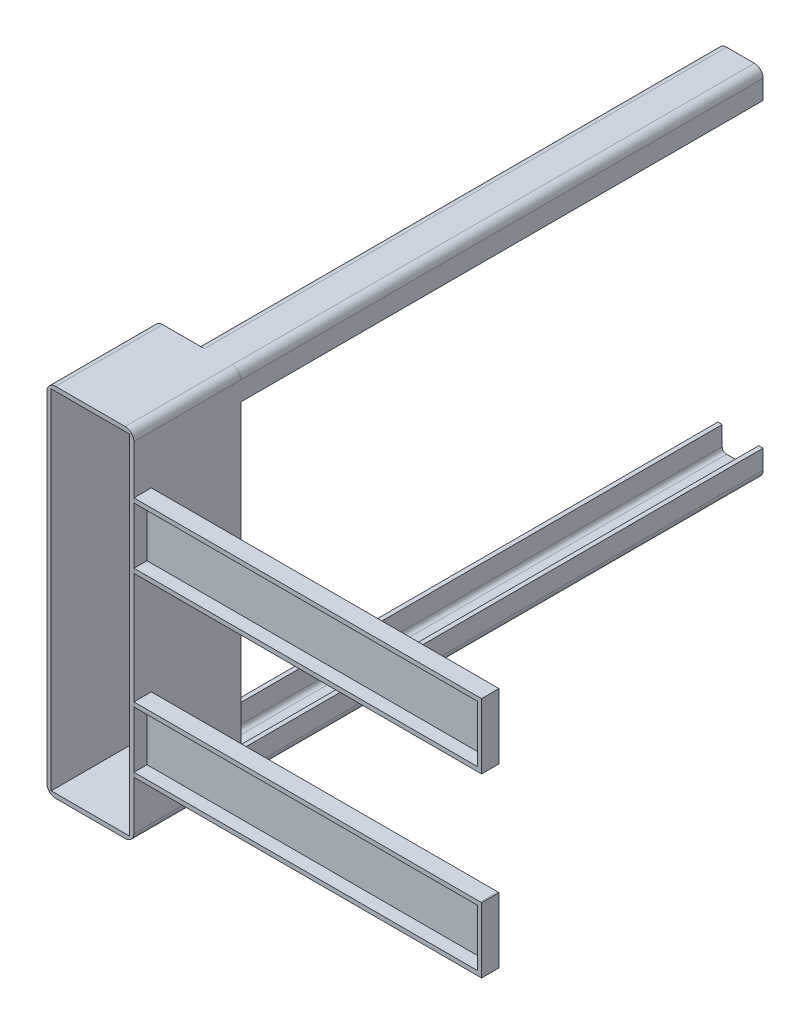
SolidWorks part; units mm, degrees
material "Alloy Steel"
ref_plane "Front Plane" through (0, 0, 0) normal (0, 0, 1) x (1, 0, 0)
ref_plane "Top Plane" through (0, 0, 0) normal (0, 1, 0) x (1, 0, 0)
ref_plane "Right Plane" through (0, 0, 0) normal (1, 0, 0) x (0, 0, -1)
sketch "Sketch1" plane through (0, 0, 0) normal (0, 0, 1) x (1, 0, 0)
  line L16 (-21, 173) -> (-26, 173)
  line L17 (16, 205) -> (-16, 205)
  line L18 (26, 195) -> (26, 173)
  line L19 (26, 173) -> (21, 173)
  line L20 (-26, 195) -> (-26, 173)
  line L21 (16, 200) -> (-16, 200)
  line L22 (21, 195) -> (21, 173)
  line L24 (-21, 195) -> (-21, 173)
  line L25 (0, 0) -> (0, 173) construction
  line L27 (-39.3633, 0) -> (62.171, 0) construction
  line L29 (-21, 173) -> (21, 173) construction
  line L30 (26, -195) -> (26, -173)
  line L31 (26, -173) -> (21, -173)
  line L32 (21, -195) -> (21, -173)
  line L33 (-21, -173) -> (-26, -173)
  line L34 (16, -205) -> (-16, -205)
  line L35 (16, -200) -> (-16, -200)
  line L36 (-26, -195) -> (-26, -173)
  line L37 (-21, -195) -> (-21, -173)
  arc A16 (26, 195) -> (16, 205) centre (16, 195) ccw
  arc A17 (-26, 195) -> (-16, 205) centre (-16, 195) cw
  arc A41 (16, 200) -> (21, 195) centre (16, 195) cw
  arc A42 (-16, 200) -> (-21, 195) centre (-16, 195) ccw
  arc A43 (16, -200) -> (21, -195) centre (16, -195) ccw
  arc A44 (26, -195) -> (16, -205) centre (16, -195) cw
  arc A45 (-26, -195) -> (-16, -205) centre (-16, -195) ccw
  arc A46 (-16, -200) -> (-21, -195) centre (-16, -195) cw
  point P34 (26, 205)
  point P39 (26, 173)
  point P44 (-21, 173)
  dimension "D5" = 10
  dimension "D8" = 32
  dimension "D3" = 5
  dimension "D6" = 52
  dimension "D11" = 205
extrude "Boss-Extrude1" add sketch "Sketch1" along normal blind 600
sketch "Sketch2" plane through (0, 0, 600) normal (0, 0, 1) x (1, 0, 0)
  line L27 (26, 205) -> (-74, 205)
  line L28 (26, 205) -> (26, -205)
  line L29 (26, -205) -> (-74, -205)
  line L30 (-74, 205) -> (-74, -205)
  line L31 (26, -195) -> (26, -173) construction
  line L32 (-16, -205) -> (16, -205) construction
  line L33 (16, 205) -> (-16, 205) construction
  dimension "D1" = 100
extrude "Boss-Extrude2" add sketch "Sketch2" along normal blind 123
sketch "Sketch37" plane through (0, 0, 600) normal (0, 0, -1) x (-1, 0, 0)
  line L0 (-26, -205) -> (-26, 173) construction
  line L1 (-26, 205) -> (74, 205) construction
  line L3 (-4, 54) -> (50, 54) construction
  line L4 (-4, 54) -> (-4, -142) construction
  line L5 (-4, -142) -> (50, -142) construction
  line L6 (50, 54) -> (50, -142) construction
  circle A0 centre (-4, -142) radius 10
  circle A1 centre (-4, 54) radius 10
  circle A2 centre (50, 54) radius 10
  circle A3 centre (50, -142) radius 10
  point P0 (-4, -142)
  dimension "D3" = 20
  dimension "D4" = 20
  dimension "D1" = 151
  dimension "D2" = 54
  dimension "D6" = 22
  dimension "D5" = 196
sketch "Sketch43" plane through (0, 0, 723) normal (0, 0, 1) x (1, 0, 0)
  line L1 (-69, 200) -> (21, 200)
  line L2 (-69, 200) -> (-69, -200)
  line L3 (-69, -200) -> (21, -200)
  line L4 (21, 200) -> (21, -200)
  line L8 (26, 205) -> (-74, 205) construction
  line L9 (26, -205) -> (26, 205) construction
  line L10 (-74, 205) -> (-74, -205) construction
  line L11 (-74, -205) -> (26, -205) construction
  dimension "D1" = 5
  dimension "D2" = 5
  dimension "D3" = 5
  dimension "D4" = 5
sketch "Sketch44" plane through (26, 0, 0) normal (1, 0, 0) x (0, 0, -1)
  line L1 (-723, 139) -> (-703, 139)
  line L2 (-723, 139) -> (-723, 64)
  line L3 (-723, 64) -> (-703, 64)
  line L4 (-703, 139) -> (-703, 64)
  line L5 (-723, 0) -> (-582.6794, 0)
  line L6 (-703, -139) -> (-703, -64)
  line L7 (-723, -64) -> (-703, -64)
  line L8 (-723, -139) -> (-723, -64)
  line L9 (-723, -139) -> (-703, -139)
  dimension "D1" = 75
  dimension "D2" = 20
  dimension "D3" = 64
extrude "Boss-Extrude16" add sketch "Sketch44" along normal blind 399.5
sketch "Sketch45" plane through (0, 139, 0) normal (0, 1, 0) x (1, 0, 0)
  line L2 (425.5, -703) -> (26, -703) construction
  line L3 (310.0576, -763.7413) -> (374.4424, -763.7413)
  line L5 (357.4487, -703) -> (327.0513, -703)
  arc A0 (327.0513, -703) -> (310.0576, -763.7413) centre (342.25, -740) ccw
  arc A1 (374.4424, -763.7413) -> (357.4487, -703) centre (342.25, -740) ccw
  point P1 (342.25, -740)
  dimension "D2" = 80
  dimension "D1" = 37
extrude "Boss-Extrude17" add sketch "Sketch45" against normal blind 278
sketch "Sketch47" plane through (0, 139, 0) normal (0, 1, 0) x (1, 0, 0)
  circle A0 centre (342.25, -740) radius 10
  dimension "D1" = 20
sketch "Sketch50" plane through (0, 0, 703) normal (0, 0, -1) x (-1, 0, 0)
  line L0 (-310.0576, 139) -> (-374.4424, 139) construction
  line L2 (-17.75, 0) -> (-475.9281, 0)
  line L3 (-383.75, 69) -> (-300.75, 69)
  line L4 (-383.75, 69) -> (-383.75, 134)
  line L5 (-383.75, 134) -> (-300.75, 134)
  line L6 (-300.75, 69) -> (-300.75, 134)
  line L7 (-383.75, 69) -> (-300.75, 134) construction
  line L8 (-383.75, 134) -> (-300.75, 69) construction
  line L10 (-383.75, -134) -> (-300.75, -69) construction
  line L11 (-383.75, -69) -> (-300.75, -134) construction
  line L12 (-300.75, -69) -> (-300.75, -134)
  line L13 (-383.75, -134) -> (-300.75, -134)
  line L14 (-383.75, -69) -> (-383.75, -134)
  line L15 (-383.75, -69) -> (-300.75, -69)
  point P0 (-342.25, 101.5)
  point P4 (-342.25, 101.5)
  point P18 (-342.25, -101.5)
  dimension "D1" = 5
  dimension "D2" = 65
  dimension "D3" = 83
extrude "Cut-Extrude19" cut sketch "Sketch37" against normal up to next (123 mm away) contours L5 A3 L6 | L6 A3 L5 | L4 A0 L5 | L5 A0 L4 | L6 A2 L3 | L3 A2 L6 | L4 A1 L3 | L3 A1 L4
extrude "Cut-Extrude20" cut sketch "Sketch43" against normal blind 118
extrude "Cut-Extrude21" cut sketch "Sketch47" against normal blind 278
sketch "Sketch54" plane through (26, 0, 0) normal (1, 0, 0) x (0, 0, -1)
  line L0 (-763.7413, -139) -> (-763.7413, 139) construction
  line L1 (-763.7413, 134) -> (-708, 134)
  line L2 (-763.7413, 134) -> (-763.7413, 69)
  line L3 (-763.7413, 69) -> (-708, 69)
  line L4 (-708, 134) -> (-708, 69)
  line L5 (-723, -64) -> (-703, -64) construction
  line L6 (-703, 139) -> (-703, 64) construction
  line L7 (-723, 64) -> (-703, 64) construction
  line L8 (-723, 139) -> (-763.7413, 139) construction
  line L9 (-708, -134) -> (-708, -69)
  line L10 (-767.5036, -69) -> (-708, -69)
  line L11 (-767.5036, -134) -> (-767.5036, -69)
  line L12 (-767.5036, -134) -> (-708, -134)
  line L13 (-703, -139) -> (-703, -64) construction
  line L14 (-723, -139) -> (-703, -139) construction
  dimension "D1" = 5
  dimension "D2" = 5
  dimension "D3" = 5
  dimension "D4" = 5
  dimension "D5" = 5
  dimension "D6" = 5
extrude "Cut-Extrude22" cut sketch "Sketch54" along normal blind 395
extrude "Cut-Extrude25" cut sketch "Sketch50" against normal blind 72 contours L3 L6 L5 L4 | L15 L14 L13 L12
sketch "Sketch55" plane through (26, 0, 0) normal (1, 0, 0) x (0, 0, -1)
  line L0 (-763.7413, -69) -> (-763.7413, 69) construction
  line L1 (-703, 64) -> (-763.7413, 64)
  line L2 (-703, 64) -> (-703, -64)
  line L3 (-703, -64) -> (-763.7413, -64)
  line L4 (-763.7413, 64) -> (-763.7413, -64)
extrude "Cut-Extrude31" cut sketch "Sketch55" along normal blind 398
fillet "Fillet3" radius 10 4 edges at (-74, -205, 661.5) (-74, 205, 661.5) (26, 205, 661.5) (26, -205, 661.5)
sketch "Sketch56" plane through (0, 0, 605) normal (0, 0, 1) x (1, 0, 0)
  circle A0 centre (-52.9744, 18.7248) radius 3.5
  circle A1 centre (4.9744, 18.7248) radius 3.5
  circle A2 centre (-52.9744, -67.8382) radius 3.5
  circle A3 centre (4.9744, -67.8382) radius 3.5
extrude "Cut-Extrude32" cut sketch "Sketch56" against normal up to surface (5 mm away) up to face at (-6, -142, 600)
sketch "Sketch57" plane through (0, -139, 0) normal (0, -1, 0) x (1, 0, 0)
  line L0 (306.0423, 723) -> (378.4577, 723)
  line L1 (310.0576, 763.7413) -> (374.4424, 763.7413) construction
  line L2 (310.0576, 763.7413) -> (374.4424, 763.7413)
  arc A0 (378.4577, 723) -> (374.4424, 763.7413) centre (342.25, 740) ccw construction
  arc A1 (310.0576, 763.7413) -> (306.0423, 723) centre (342.25, 740) ccw construction
  arc A2 (378.4577, 723) -> (374.4424, 763.7413) centre (342.25, 740) ccw
  arc A3 (310.0576, 763.7413) -> (306.0423, 723) centre (342.25, 740) ccw
extrude "Cut-Extrude33" cut sketch "Sketch57" against normal through all both and the other way through all
sketch "Sketch58" plane through (0, 0, 703) normal (0, 0, -1) x (-1, 0, 0)
  line L0 (-383.75, -69) -> (-300.75, -69) construction
  line L1 (-383.75, -69) -> (-383.75, -134) construction
  line L2 (-383.75, -134) -> (-300.75, -134) construction
  line L3 (-300.75, -69) -> (-300.75, -134) construction
  line L4 (-383.75, -69) -> (-300.75, -69)
  line L5 (-383.75, -69) -> (-383.75, -134)
  line L6 (-383.75, -134) -> (-300.75, -134)
  line L7 (-300.75, -69) -> (-300.75, -134)
  line L8 (-383.75, 134) -> (-300.75, 134) construction
  line L9 (-383.75, 69) -> (-383.75, 134) construction
  line L10 (-383.75, 69) -> (-300.75, 69) construction
  line L11 (-300.75, 69) -> (-300.75, 134) construction
  line L12 (-383.75, 134) -> (-300.75, 134)
  line L13 (-383.75, 69) -> (-383.75, 134)
  line L14 (-383.75, 69) -> (-300.75, 69)
  line L15 (-300.75, 69) -> (-300.75, 134)
  dimension "D1" = 65
  dimension "D2" = 83
extrude "Boss-Extrude18" add sketch "Sketch58" against normal blind 5
